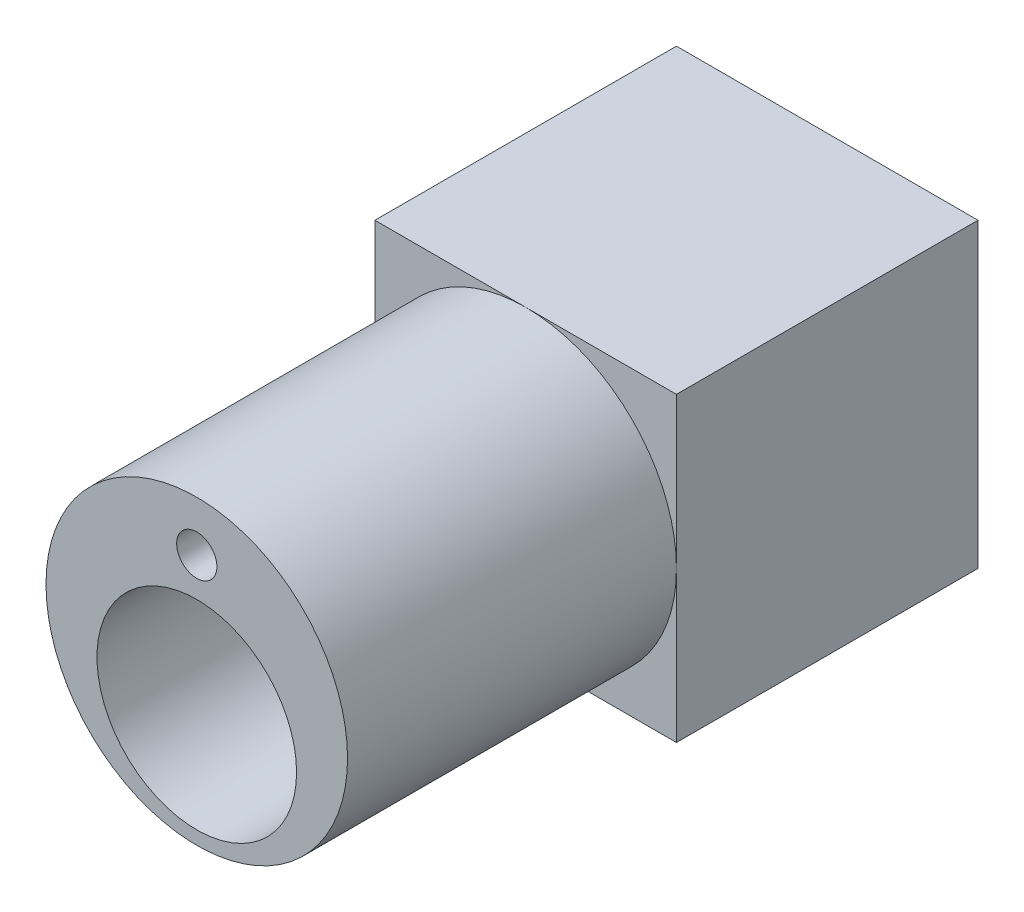
SolidWorks part; units mm, degrees
ref_plane "Front Plane" through (0, 0, 0) normal (0, 0, 1) x (1, 0, 0)
ref_plane "Top Plane" through (0, 0, 0) normal (0, 1, 0) x (1, 0, 0)
ref_plane "Right Plane" through (0, 0, 0) normal (1, 0, 0) x (0, 0, -1)
sketch "Sketch1" plane through (0, 0, 0) normal (0, 0, 1) x (1, 0, 0)
  circle A0 centre (0, 0) radius 28.1
extrude "Boss-Extrude2" add sketch "Sketch1" along normal blind 61.3
sketch "Sketch3" plane through (0, 0, 61.3) normal (0, 0, 1) x (1, 0, 0)
  circle A1 centre (0, -7) radius 18.6
extrude "Cut-Extrude2" cut sketch "Sketch3" against normal blind 58.8 contours A1
sketch "Sketch4" plane through (0, 0, 0) normal (0, 0, -1) x (-1, 0, 0)
  line L1 (-28.1, -28.1) -> (28.1, -28.1)
  line L2 (-28.1, -28.1) -> (-28.1, 28.1)
  line L3 (-28.1, 28.1) -> (28.1, 28.1)
  line L4 (28.1, -28.1) -> (28.1, 28.1)
  line L5 (-28.1, -28.1) -> (28.1, 28.1) construction
  line L6 (-28.1, 28.1) -> (28.1, -28.1) construction
  point P0 (0, 0)
extrude "Boss-Extrude3" add sketch "Sketch4" along normal blind 56.2
sketch "Sketch5" plane through (0, 0, 2.5) normal (0, 0, 1) x (1, 0, 0)
  circle A1 centre (0, -7) radius 16.1
extrude "Cut-Extrude4" cut sketch "Sketch5" against normal blind 5
sketch "Sketch6" plane through (0, 0, -56.2) normal (0, 0, -1) x (-1, 0, 0)
  line L1 (-24.8987, -24.8896) -> (24.8987, -24.8896)
  line L2 (-24.8987, -24.8896) -> (-24.8987, 24.8896)
  line L3 (-24.8987, 24.8896) -> (24.8987, 24.8896)
  line L4 (24.8987, -24.8896) -> (24.8987, 24.8896)
  line L5 (-24.8987, -24.8896) -> (24.8987, 24.8896) construction
  line L6 (-24.8987, 24.8896) -> (24.8987, -24.8896) construction
  point P0 (0, 0)
extrude "Cut-Extrude5" cut sketch "Sketch6" against normal blind 53.7
sketch "Sketch7" plane through (0, -28.1, 0) normal (0, -1, 0) x (-1, 0, 0)
  circle A0 centre (0, 28.1) radius 28.1
extrude "Boss-Extrude4" add sketch "Sketch7" along normal blind 321.5 contours A0
sketch "Sketch8" plane through (0, -349.6, 0) normal (0, -1, 0) x (-1, 0, 0)
  line L1 (-1.6583, 25.8321) -> (1.6583, 25.8321)
  line L3 (-1.6583, 30.8321) -> (1.6583, 30.8321)
  arc A2 (-1.6583, 30.8321) -> (-1.6583, 25.8321) centre (0, 28.3321) ccw
  arc A3 (1.6583, 25.8321) -> (1.6583, 30.8321) centre (0, 28.3321) ccw
extrude "Cut-Extrude6" cut sketch "Sketch8" against normal blind 10
sketch "Sketch9" plane through (0, -349.6, 0) normal (0, -1, 0) x (-1, 0, 0)
  circle A1 centre (0, 28.3321) radius 3
extrude "Cut-Extrude7" cut sketch "Sketch9" against normal blind 1
sketch "Sketch10" plane through (0, -349.6, 0) normal (0, -1, 0) x (-1, 0, 0)
  circle A1 centre (0, 28.3321) radius 6.025
extrude "Cut-Extrude8" cut sketch "Sketch10" against normal blind 0.1
sketch "Sketch15" plane through (0, -349.6, 0) normal (0, -1, 0) x (-1, 0, 0)
  line L0 (6.025, 28.3321) -> (-6.025, 28.3321)
  circle A0 centre (0, 28.3321) radius 6.025 construction
  arc A1 (15, 28.3321) -> (-15, 28.3321) centre (0, 28.3321) ccw
sketch3d "3DSketch2"
  line L1 (-15, -349.6, -28.3321) -> (-22.5, -349.6, -28.3321)
  line L2 (-15, -349.6, -28.3321) -> (-15, -20, -28.3321)
  line L3 (-15, -20, -28.3321) -> (-22.5, -20, -28.3321)
  line L4 (-22.5, -349.6, -28.3321) -> (-22.5, -20, -28.3321)
sweep "Cut-Sweep4" cut profiles "3DSketch2" path "Sketch15"
sketch "Sketch18" plane through (0, 0, 61.3) normal (0, 0, 1) x (1, 0, 0)
  circle A1 centre (0, 18.75) radius 3.75
extrude "Cut-Extrude9" cut sketch "Sketch18" against normal blind 100
sketch "Sketch19" plane through (0, -349.6, 0) normal (0, -1, 0) x (-1, 0, 0)
  circle A0 centre (-18.75, 28.3321) radius 3.75
  circle A1 centre (18.75, 28.3321) radius 3.75
extrude "Cut-Extrude11" cut sketch "Sketch19" against normal blind 325
sketch "Sketch20" plane through (0, 0, -56.2) normal (0, 0, -1) x (-1, 0, 0)
  line L0 (-28.1, -28.1) -> (0, -28.1) construction
  line L5 (-28.1, -28.1) -> (57.9013, -28.1)
  line L6 (-28.1, -28.1) -> (-28.1, -407.3833)
  line L7 (-28.1, -407.3833) -> (57.9013, -407.3833)
  line L8 (57.9013, -28.1) -> (57.9013, -407.3833)
extrude "Cut-Extrude16" cut sketch "Sketch20" against normal blind 171.5
